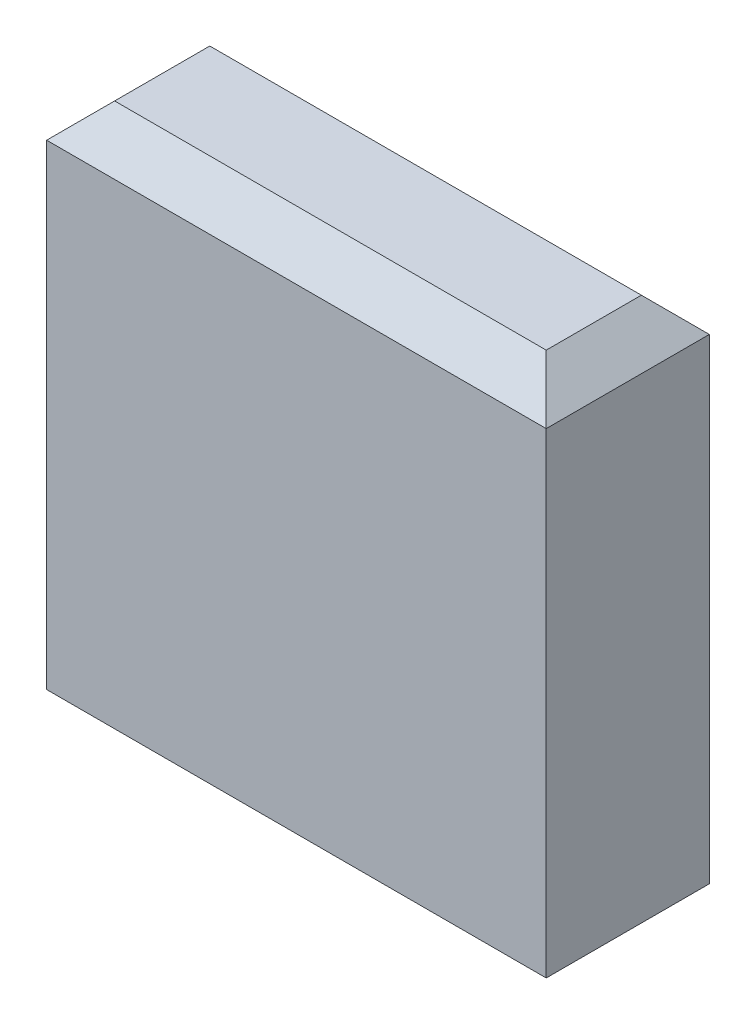
SolidWorks part; units mm, degrees
ref_plane "Front Plane" through (0, 0, 0) normal (0, 0, 1) x (1, 0, 0)
ref_plane "Top Plane" through (0, 0, 0) normal (0, 1, 0) x (1, 0, 0)
ref_plane "Right Plane" through (0, 0, 0) normal (1, 0, 0) x (0, 0, -1)
sketch "Sketch1" plane through (0, 0, 0) normal (0, 1, 0) x (1, 0, 0)
  line L1 (7.35, 2.4) -> (-7.35, 2.4)
  line L2 (7.35, 2.4) -> (7.35, -2.4)
  line L3 (7.35, -2.4) -> (-7.35, -2.4)
  line L4 (-7.35, 2.4) -> (-7.35, -2.4)
  line L5 (7.35, 2.4) -> (-7.35, -2.4) construction
  line L6 (7.35, -2.4) -> (-7.35, 2.4) construction
  point P0 (0, 0)
  dimension "D1" = 4.8
  dimension "D2" = 14.7
extrude "Boss-Extrude1" add sketch "Sketch1" along normal blind 15
chamfer "Chamfer1" distance 1 angle 45 4 edges at (0, 15, -2.4) (7.35, 15, 0) (0, 15, 2.4) (-7.35, 15, 0)
